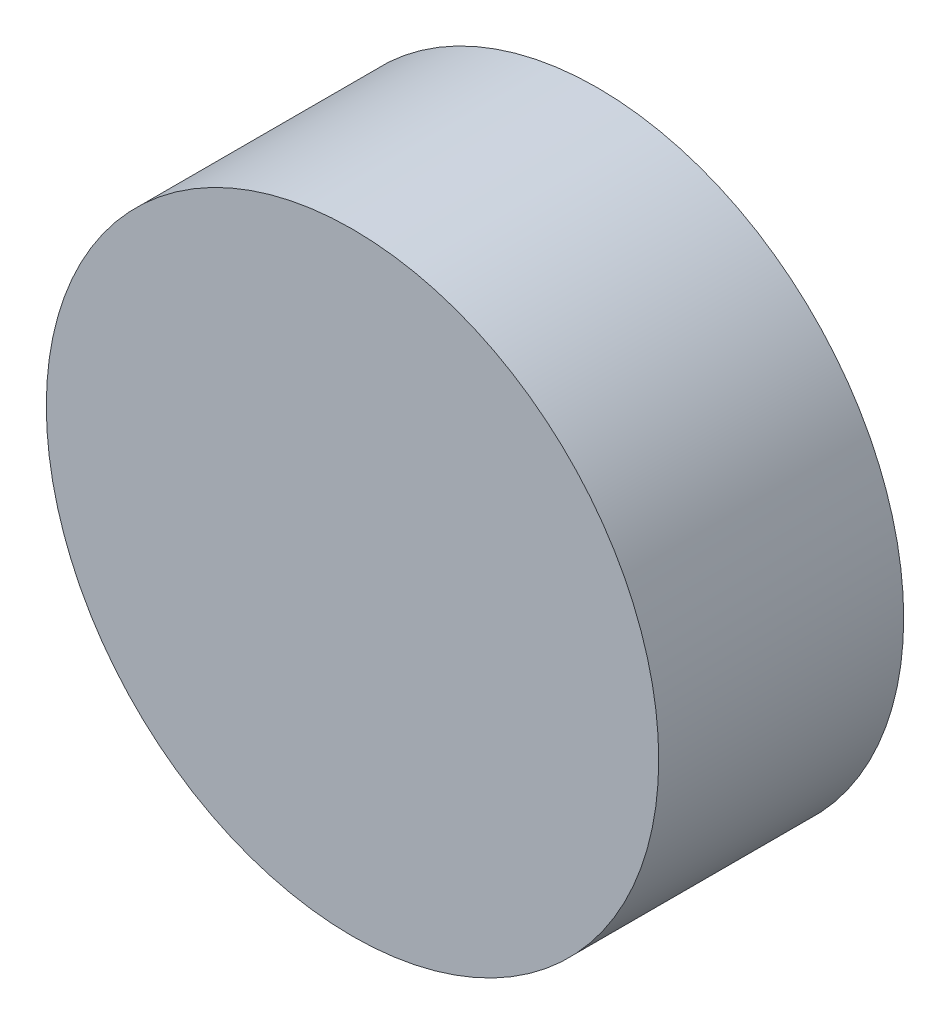
SolidWorks part; units mm, degrees
ref_plane "前视基准面" through (0, 0, 0) normal (0, 0, 1) x (1, 0, 0)
ref_plane "上视基准面" through (0, 0, 0) normal (0, 1, 0) x (1, 0, 0)
ref_plane "右视基准面" through (0, 0, 0) normal (1, 0, 0) x (0, 0, -1)
sketch "草图1" plane through (0, 0, 0) normal (0, 0, 1) x (1, 0, 0)
  circle A0 centre (0, 0) radius 2.5
  dimension "D1" = 5
extrude "凸台-拉伸1" add sketch "草图1" along normal blind 2 contours A0
